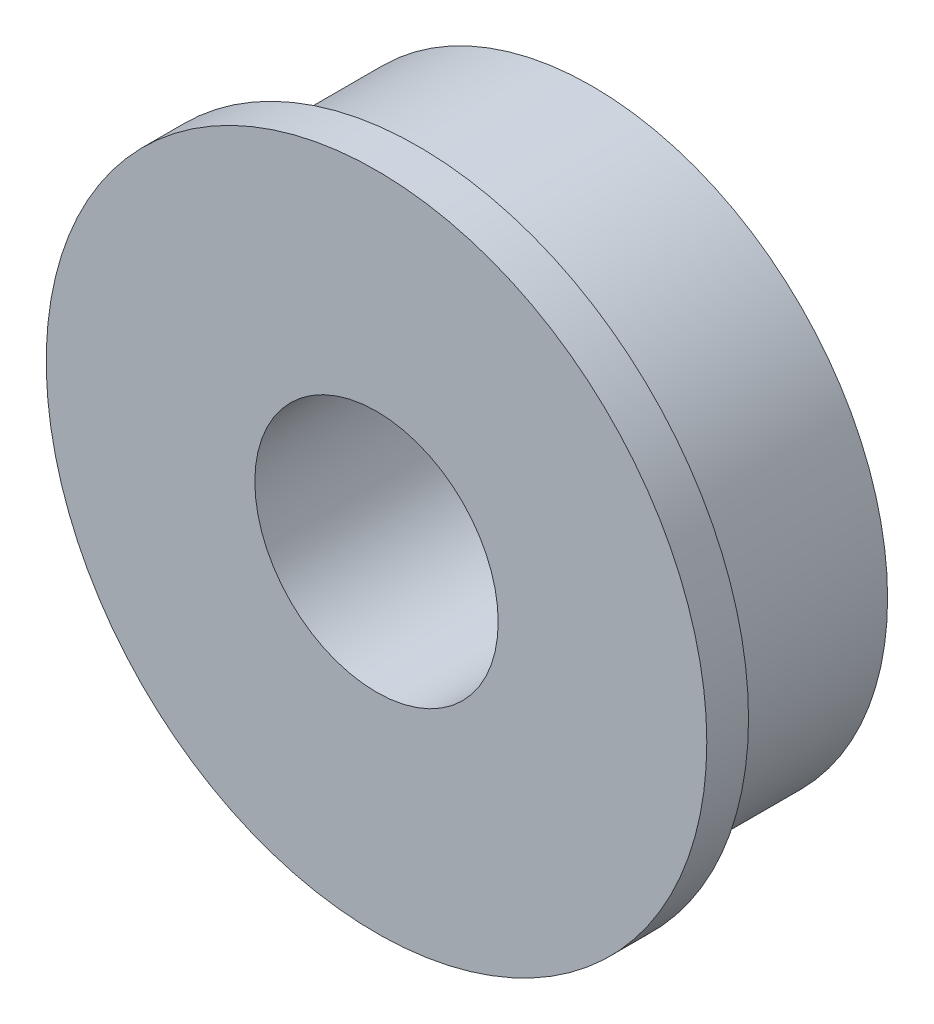
SolidWorks part; units mm, degrees
ref_plane "前基準面" through (0, 0, 0) normal (0, 0, 1) x (1, 0, 0)
ref_plane "上基準面" through (0, 0, 0) normal (0, 1, 0) x (1, 0, 0)
ref_plane "右基準面" through (0, 0, 0) normal (1, 0, 0) x (0, 0, -1)
sketch "草圖1" plane through (0, 0, 0) normal (0, 0, 1) x (1, 0, 0)
  circle A0 centre (0, 0) radius 8.5
  dimension "D1" = 17
extrude "填料-伸長1" add sketch "草圖1" along normal blind 5
sketch "草圖2" plane through (0, 0, 5) normal (0, 0, 1) x (1, 0, 0)
  circle A0 centre (0, 0) radius 9.5
  dimension "D1" = 19
extrude "填料-伸長2" add sketch "草圖2" along normal blind 1.2
sketch "草圖3" plane through (0, 0, 6.2) normal (0, 0, 1) x (1, 0, 0)
  circle A0 centre (0, 0) radius 3.5
  dimension "D1" = 7
extrude "除料-伸長1" cut sketch "草圖3" against normal up to next
